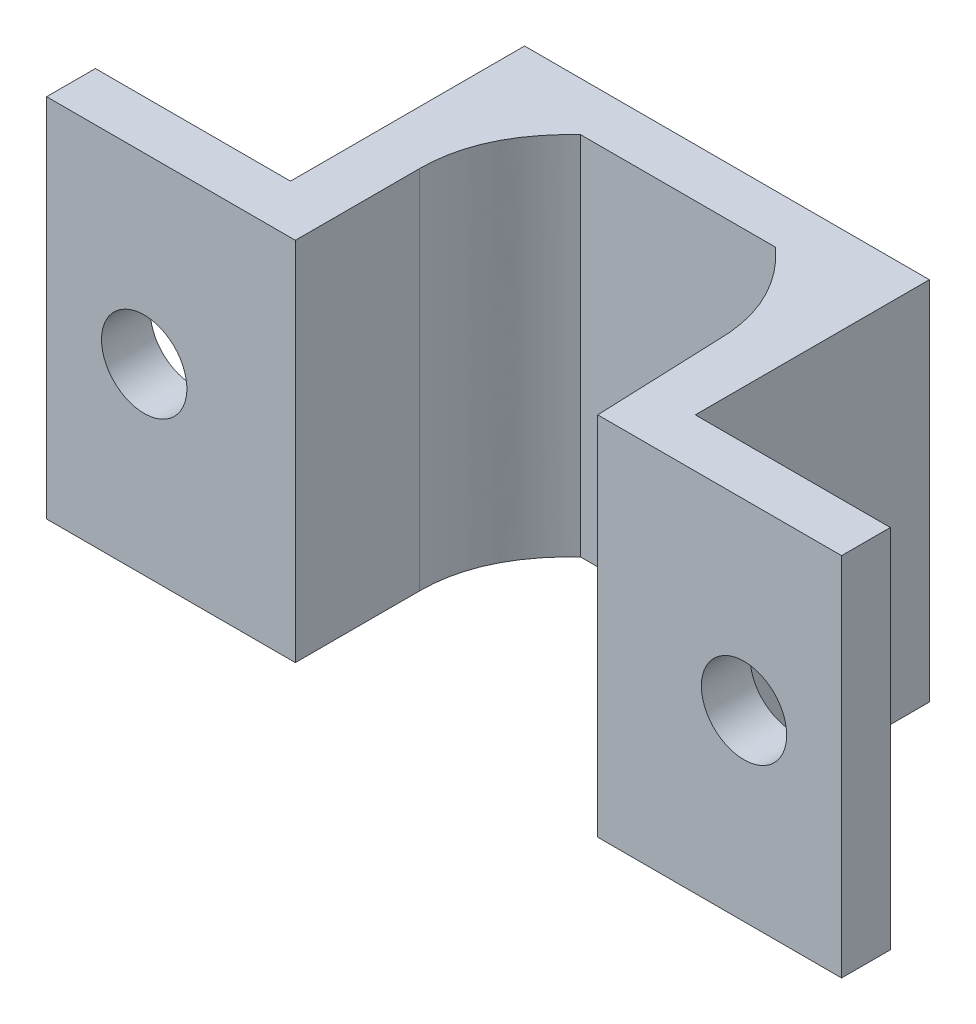
SolidWorks part; units mm, degrees
ref_plane "Front Plane" through (0, 0, 0) normal (0, 0, 1) x (1, 0, 0)
ref_plane "Top Plane" through (0, 0, 0) normal (0, 1, 0) x (1, 0, 0)
ref_plane "Right Plane" through (0, 0, 0) normal (1, 0, 0) x (0, 0, -1)
sketch "Sketch1" plane through (0, 0, 0) normal (0, 1, 0) x (1, 0, 0)
  line L0 (12.4, 5.1) -> (12.6, 0)
  line L1 (2.3, 9.6) -> (10.3, 9.6)
  line L2 (0, 0) -> (-10, 0)
  line L3 (-10, 0) -> (-10, 2)
  line L4 (-10, 2) -> (-2, 2)
  line L5 (-2, 2) -> (-2, 11.6)
  line L6 (-2, 11.6) -> (14.6, 11.6)
  line L7 (6.3, 11.6) -> (6.3, 0.824) construction
  line L8 (14.6, 2) -> (14.6, 11.6)
  line L9 (22.6, 2) -> (14.6, 2)
  line L10 (22.6, 0) -> (22.6, 2)
  line L11 (12.6, 0) -> (22.6, 0)
  line L12 (0.2, 5.1) -> (0.2, 0)
  line L13 (0.2, 0) -> (0, 0)
  spline S0 degree 2 poles (2.3, 9.6) (0.2, 7.65) (0.2, 5.1) knots 0 0 0 0.5 0.5 0.5
  spline S1 degree 2 poles (10.3, 9.6) (12.4, 7.65) (12.4, 5.1) knots 0 0 0 0.5 0.5 0.5
  point P16 (6.3, 9.6)
  dimension "D1" = 12.2
  dimension "D2" = 4
  dimension "D3" = 9.6
  dimension "D4" = 2
  dimension "D5" = 32.6
  dimension "D6" = 2
  dimension "D7" = 8
extrude "Boss-Extrude1" add sketch "Sketch1" along normal blind 15
sketch "Sketch2" plane through (0, 0, -2) normal (0, 0, -1) x (-1, 0, 0)
  line L2 (-22.6, 15) -> (-22.6, 0) construction
  line L3 (-22.6, 15) -> (-14.6, 15) construction
  line L4 (10, 15) -> (10, 0) construction
  line L5 (2, 0) -> (10, 0) construction
  circle A0 centre (-18.6, 7.5) radius 1.75
  circle A1 centre (6, 7.5) radius 1.75
  dimension "D1" = 3.5
  dimension "D4" = 3.5
  dimension "D2" = 4
  dimension "D3" = 7.5
  dimension "D5" = 4
  dimension "D6" = 7.5
extrude "Cut-Extrude1" cut sketch "Sketch2" against normal blind 15
